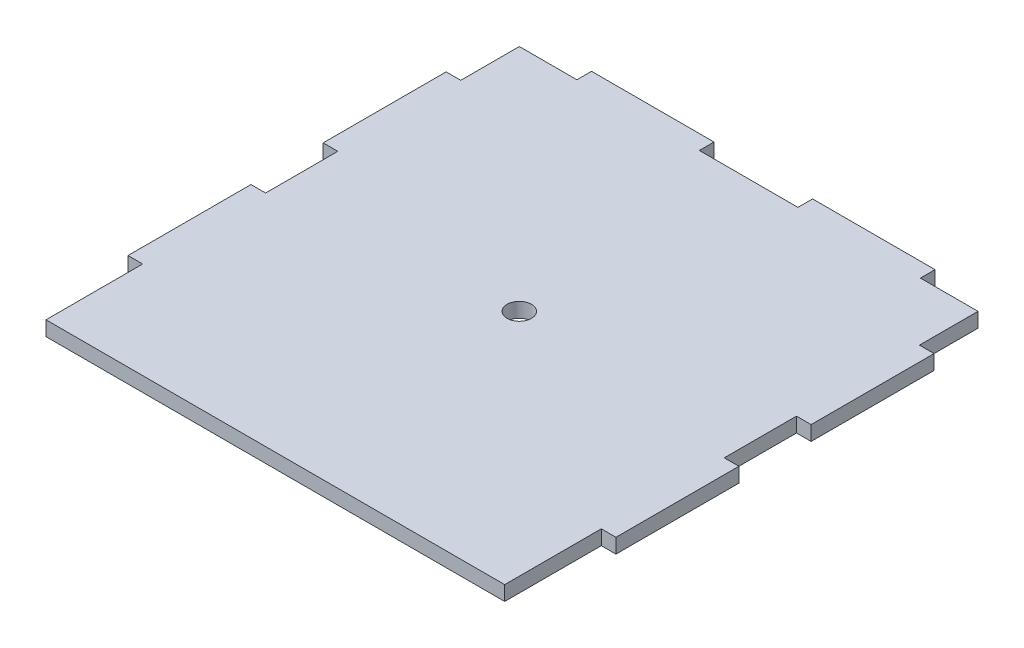
SolidWorks part; units mm, degrees
ref_plane "Front Plane" through (0, 0, 0) normal (0, 0, 1) x (1, 0, 0)
ref_plane "Top Plane" through (0, 0, 0) normal (0, 1, 0) x (1, 0, 0)
ref_plane "Right Plane" through (0, 0, 0) normal (1, 0, 0) x (0, 0, -1)
sketch "Sketch1" plane through (0, 0, 0) normal (0, 1, 0) x (1, 0, 0)
  line L0 (-900, 50) -> (49100, 50) construction
  line L1 (0, 0) -> (100, 0)
  line L2 (0, 0) -> (0, 100)
  line L3 (0, 100) -> (100, 100)
  line L4 (100, 0) -> (100, 100)
  line L5 (50, -900) -> (50, 49100) construction
  line L6 (100, 100) -> (85.2, 100)
  line L11 (0, 97) -> (14.8, 97)
  line L12 (0, 97) -> (0, 100)
  line L13 (0, 100) -> (14.8, 100)
  line L14 (14.8, 97) -> (14.8, 100)
  line L15 (85.2, 97) -> (85.2, 100)
  line L16 (100, 97) -> (85.2, 97)
  line L17 (100, 97) -> (100, 100)
  line L18 (3, 19.8) -> (0, 19.8)
  line L19 (39.9, 100) -> (60.1, 100)
  line L20 (39.9, 100) -> (39.9, 97)
  line L21 (39.9, 97) -> (60.1, 97)
  line L22 (60.1, 100) -> (60.1, 97)
  line L23 (97, 0) -> (100, 0)
  line L24 (97, 0) -> (97, 19.8)
  line L25 (97, 19.8) -> (100, 19.8)
  line L26 (100, 0) -> (100, 19.8)
  line L27 (100, 45) -> (97, 45)
  line L28 (100, 45) -> (100, 59.8)
  line L29 (100, 59.8) -> (97, 59.8)
  line L30 (97, 45) -> (97, 59.8)
  line L31 (97, 97) -> (100, 97)
  line L32 (97, 97) -> (97, 85)
  line L33 (97, 85) -> (100, 85)
  line L34 (100, 97) -> (100, 85)
  line L35 (0, 0) -> (0, 19.8)
  line L36 (3, 0) -> (0, 0)
  line L37 (3, 0) -> (3, 19.8)
  line L38 (0, 59.8) -> (3, 59.8)
  line L39 (3, 45) -> (3, 59.8)
  line L40 (0, 45) -> (3, 45)
  line L41 (0, 45) -> (0, 59.8)
  line L42 (3, 85) -> (0, 85)
  line L43 (0, 97) -> (0, 85)
  line L44 (3, 97) -> (0, 97)
  line L45 (3, 97) -> (3, 85)
  circle A0 centre (50, 50) radius 2.5
  point P8 (100, 50)
  point P9 (50, 50)
  point P11 (50, 100)
  dimension "D3" = 5
  dimension "D1" = 100
  dimension "D2" = 100
  dimension "D4" = 14.8
  dimension "D5" = 3
  dimension "D6" = 25.1
  dimension "D7" = 20.2
  dimension "D8" = 3
  dimension "D9" = 3
  dimension "D10" = 3
  dimension "D11" = 3
  dimension "D12" = 25.2
  dimension "D13" = 25.2
  dimension "D14" = 19.8
  dimension "D15" = 14.8
extrude "Boss-Extrude1" add sketch "Sketch1" along normal blind 3 contours L11 L45 L42 L2 L38 L39 L40 L18 L37 L1 L24 L25 L4 L27 L30 L29 L33 L32 L16 L15 L3 L22 L21 L20 L14 A0
